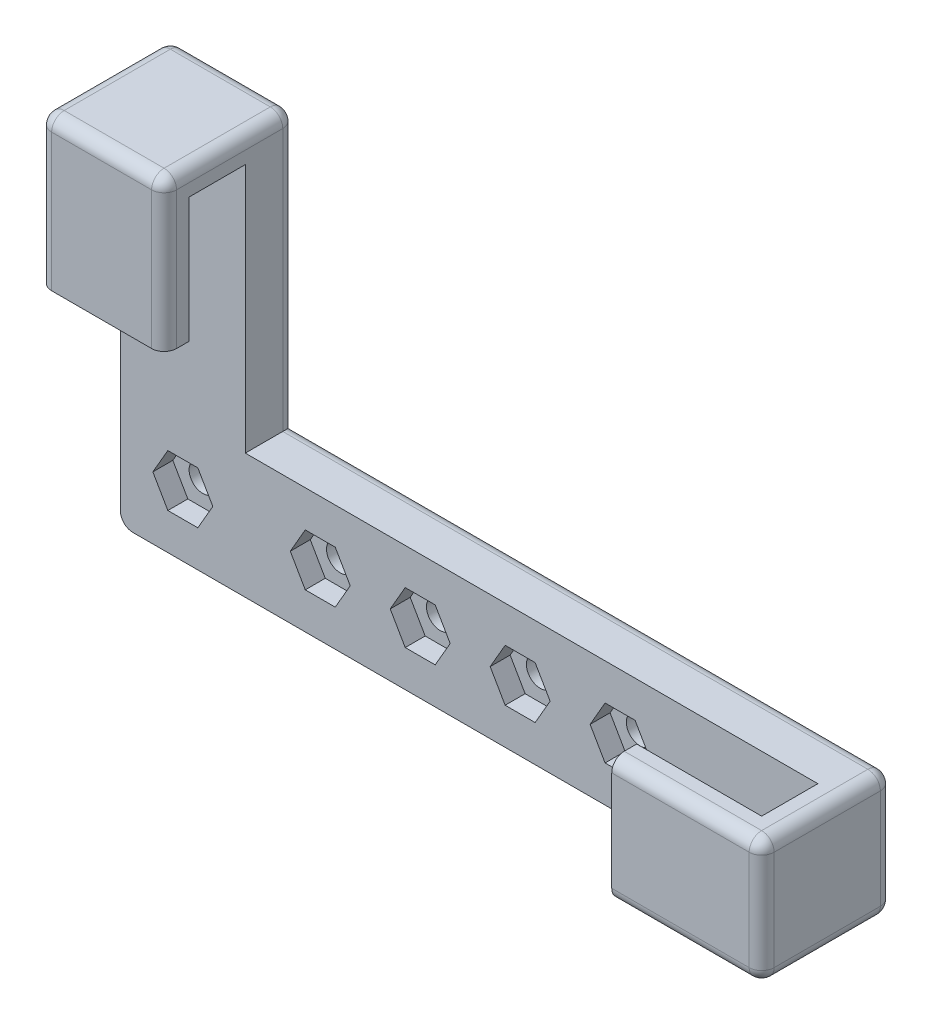
SolidWorks part; units mm, degrees
ref_plane "Plan de face" through (0, 0, 0) normal (0, 0, 1) x (1, 0, 0)
ref_plane "Plan de dessus" through (0, 0, 0) normal (0, 1, 0) x (1, 0, 0)
ref_plane "Plan de droite" through (0, 0, 0) normal (1, 0, 0) x (0, 0, -1)
sketch "Esquisse1" plane through (0, 0, 0) normal (0, 1, 0) x (1, 0, 0)
  line L0 (19.8322, -6.5) -> (31.8322, -6.5)
  line L1 (31.8322, -6.5) -> (31.8322, 4)
  line L3 (19.8322, -6.5) -> (19.8322, -4.5)
  line L4 (19.8322, -4.5) -> (29.8322, -4.5)
  line L5 (29.8322, -4.5) -> (29.8322, 0)
  line L6 (29.8322, 0) -> (-26, 0)
  line L7 (31.8322, 4) -> (-26, 4)
  line L8 (-26, 4) -> (-26, 0)
  dimension "D6" = 57.8322
  dimension "D7" = 26
  dimension "D1" = 10
  dimension "D2" = 4
  dimension "D3" = 2
  dimension "D4" = 2
  dimension "D5" = 10.5
  dimension "D8" = 4.5
extrude "Boss.-Extru.1" add sketch "Esquisse1" along normal blind 10
sketch "Esquisse4" plane through (-26, 0, 0) normal (-1, 0, 0) x (0, 0, 1)
  line L1 (-4, 10) -> (0, 10)
  line L2 (-4, 10) -> (-4, 32)
  line L3 (-4, 32) -> (6.5, 32)
  line L5 (0, 10) -> (0, 30)
  line L6 (0, 30) -> (4.5, 30)
  line L7 (4.5, 30) -> (4.5, 20)
  line L8 (4.5, 20) -> (6.5, 20)
  line L9 (6.5, 20) -> (6.5, 32)
  dimension "D1" = 22
  dimension "D2" = 4.5
  dimension "D3" = 10
  dimension "D4" = 2
  dimension "D5" = 2
extrude "Boss.-Extru.2" add sketch "Esquisse4" against normal blind 10
fillet "Congé1" radius 1 17 edges at (2.9161, 0, -4) (31.8322, 5, 6.5) (31.8322, 0, 1.25) (31.8322, 10, 1.25) (-26, 0, -2) (7.9161, 10, -4) (-21, 32, 6.5) (-16, 32, 1.25) (-21, 32, -4) (-26, 32, 1.25) (-26, 16, -4) (-16, 21, -4) (25.8322, 0, 6.5) (25.8322, 10, 6.5) (-26, 26, 6.5) (-16, 26, 6.5) (31.8322, 5, -4)
sketch "Esquisse5" plane through (0, 0, -4) normal (0, 0, -1) x (-1, 0, 0)
  line L3 (-30.8322, 10) -> (16, 10) construction
  line L4 (25, 0) -> (-30.8322, 0) construction
  line L5 (16, 10) -> (16, 31) construction
  line L7 (26, 31) -> (26, 1) construction
  line L8 (-31.8322, 1) -> (-31.8322, 9) construction
  circle A0 centre (10, 5) radius 1.1
  circle A1 centre (2, 5) radius 1.1
  circle A2 centre (-6, 5) radius 1.1
  circle A3 centre (-14, 5) radius 1.1
  circle A4 centre (21, 5) radius 1.1
  dimension "D1" = 2.2
  dimension "D2" = 8
  dimension "D3" = 8
  dimension "D4" = 8
  dimension "D5" = 5
  dimension "D6" = 5
  dimension "D7" = 6
  dimension "D8" = 17.8322
  dimension "D9" = 16
  dimension "D10" = 5
  dimension "D11" = 5
extrude "Enlèv. mat.-Extru.1" cut sketch "Esquisse5" against normal up to next
sketch "Esquisse6" plane through (0, 0, 0) normal (0, 0, 1) x (1, 0, 0)
  line L0 (-16, 10) -> (29.8322, 10) construction
  line L1 (12.8, 7.0785) -> (11.6, 5)
  line L2 (11.6, 5) -> (12.8, 2.9215)
  line L3 (12.8, 2.9215) -> (15.2, 2.9215)
  line L4 (15.2, 2.9215) -> (16.4, 5)
  line L5 (16.4, 5) -> (15.2, 7.0785)
  line L6 (15.2, 7.0785) -> (12.8, 7.0785)
  line L7 (4.8, 7.0785) -> (3.6, 5)
  line L8 (3.6, 5) -> (4.8, 2.9215)
  line L9 (4.8, 2.9215) -> (7.2, 2.9215)
  line L10 (7.2, 2.9215) -> (8.4, 5)
  line L11 (8.4, 5) -> (7.2, 7.0785)
  line L12 (7.2, 7.0785) -> (4.8, 7.0785)
  line L13 (-3.2, 7.0785) -> (-4.4, 5)
  line L14 (-4.4, 5) -> (-3.2, 2.9215)
  line L15 (-3.2, 2.9215) -> (-0.8, 2.9215)
  line L16 (-0.8, 2.9215) -> (0.4, 5)
  line L17 (0.4, 5) -> (-0.8, 7.0785)
  line L18 (-0.8, 7.0785) -> (-3.2, 7.0785)
  line L19 (-11.2, 7.0785) -> (-12.4, 5)
  line L20 (-12.4, 5) -> (-11.2, 2.9215)
  line L21 (-11.2, 2.9215) -> (-8.8, 2.9215)
  line L22 (-8.8, 2.9215) -> (-7.6, 5)
  line L23 (-7.6, 5) -> (-8.8, 7.0785)
  line L24 (-8.8, 7.0785) -> (-11.2, 7.0785)
  line L26 (-22.2, 7.0785) -> (-23.4, 5)
  line L27 (-23.4, 5) -> (-22.2, 2.9215)
  line L28 (-22.2, 2.9215) -> (-19.8, 2.9215)
  line L29 (-19.8, 2.9215) -> (-18.6, 5)
  line L30 (-18.6, 5) -> (-19.8, 7.0785)
  line L31 (-19.8, 7.0785) -> (-22.2, 7.0785)
  circle A0 centre (14, 5) radius 2.0785 construction
  circle A1 centre (6, 5) radius 2.0785 construction
  circle A2 centre (-2, 5) radius 2.0785 construction
  circle A3 centre (-10, 5) radius 2.0785 construction
  circle A4 centre (-21, 5) radius 2.0785 construction
  dimension "D1" = 2.4
extrude "Enlèv. mat.-Extru.2" cut sketch "Esquisse6" against normal blind 1.6
